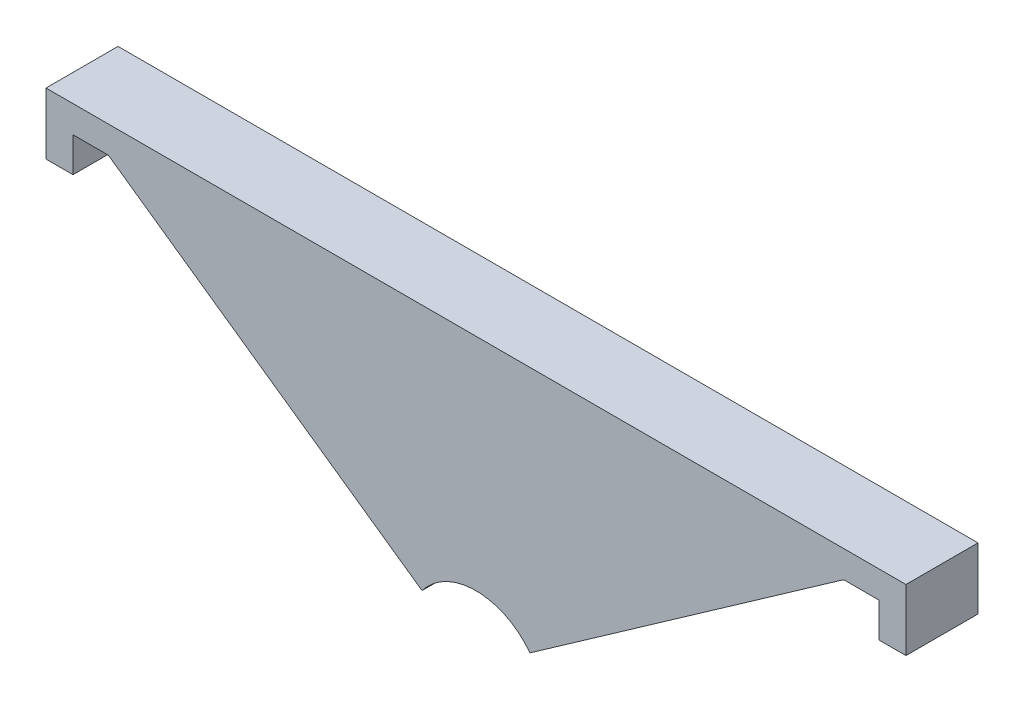
SolidWorks part; units mm, degrees
ref_plane "Plan de face" through (0, 0, 0) normal (0, 0, 1) x (1, 0, 0)
ref_plane "Plan de dessus" through (0, 0, 0) normal (0, 1, 0) x (1, 0, 0)
ref_plane "Plan de droite" through (0, 0, 0) normal (1, 0, 0) x (0, 0, -1)
sketch "Esquisse1" plane through (0, 0, 0) normal (0, 0, 1) x (1, 0, 0)
  line L0 (0, 0) -> (0, 20.2323) construction
  line L2 (-56.5, 0) -> (-56.5, 5) construction
  line L3 (-56.5, 5) -> (-44.5, 5) construction
  line L4 (-44.5, 13.3425) -> (-44.5, 72.3618) construction
  line L11 (-56.5, 0) -> (-35.792, 0) construction
  line L28 (-13.1159, 49.7073) -> (-44.5, 5) construction
  line L29 (-35.792, 0) -> (-21.7522, 20) construction
  line L30 (35.792, 0) -> (21.7522, 20) construction
  line L31 (13.1159, 49.7073) -> (44.5, 5) construction
  line L32 (56.5, 0) -> (35.792, 0) construction
  line L33 (56.5, 5) -> (44.5, 5) construction
  line L34 (56.5, 0) -> (56.5, 5) construction
  line L35 (-21.7522, 20) -> (21.7522, 20) construction
  line L36 (44.5, 5) -> (15.9887, 45.6149) construction
  line L37 (0, 40.5) -> (13.1159, 49.7073) construction
  line L49 (-44.5, 65.6296) -> (-44.5, 69.2189) construction
  line L50 (-44.5, 69.2189) -> (-40.9107, 69.2189) construction
  line L51 (-40.9107, 69.2189) -> (-13.1159, 49.7073) construction
  line L52 (-15.9887, 45.6149) -> (-44.5, 65.6296) construction
  line L54 (-44.5, 5) -> (-15.9887, 45.6149) construction
  line L55 (-13.1159, 49.7073) -> (-6.1385, 44.8092) construction
  line L56 (6.1385, 44.8092) -> (13.1159, 49.7073) construction
  line L57 (44.5, 65.6296) -> (44.5, 69.2189) construction
  line L58 (44.5, 69.2189) -> (40.9107, 69.2189) construction
  line L59 (15.9887, 45.6149) -> (44.5, 65.6296) construction
  line L60 (40.9107, 69.2189) -> (13.1159, 49.7073) construction
  line L61 (-17.0873, 35.3475) -> (-25.8445, 22.8728) construction
  line L62 (-25.8445, 22.8728) -> (-3.3233, 22.8728) construction
  line L63 (-21.7522, 20) -> (-29.9368, 25.7456) construction
  line L64 (-3.3233, 22.8728) -> (-3.3233, 25.8728) construction
  line L65 (-17.0873, 35.3475) -> (-14.0873, 35.3475) construction
  line L66 (0, 40.5) -> (0, 56.525) construction
  line L67 (17.0873, 35.3475) -> (14.0873, 35.3475) construction
  line L68 (3.3233, 22.8728) -> (3.3233, 25.8728) construction
  line L69 (25.8445, 22.8728) -> (3.3233, 22.8728) construction
  line L70 (17.0873, 35.3475) -> (25.8445, 22.8728) construction
  circle A1 centre (0, 40.5) radius 11.025 construction
  arc A3 (13.1159, 49.7073) -> (-13.1159, 49.7073) centre (0, 40.5) ccw construction
  circle A5 centre (0, 40.5) radius 7 construction
  arc A6 (-6.1385, 44.8092) -> (6.1385, 44.8092) centre (0, 40.5) ccw construction
  arc A7 (-3.3233, 25.8728) -> (-14.0873, 35.3475) centre (0, 40.5) cw construction
  arc A8 (3.3233, 25.8728) -> (14.0873, 35.3475) centre (0, 40.5) ccw construction
  point P17 (0, 20)
  dimension "D1" = 22.05
  dimension "D5" = 5
  dimension "D9" = 14
  dimension "D10" = 0.5
  dimension "D12" = 15
  dimension "D2" = 40.5
  dimension "D3" = 5
  dimension "D4" = 12
  dimension "D6" = 10
  dimension "D7" = 56.5
  dimension "D8" = 20
  dimension "D11" = 5
  dimension "D13" = 3
sketch "Esquisse2" plane through (0, 0, 0) normal (0, 0, 1) x (1, 0, 0)
  line L0 (-47.75, 65.6296) -> (-44.75, 65.6296)
  line L1 (0, 40.5) -> (0, 56.525) construction
  line L2 (-44.75, 65.6296) -> (-44.75, 69.4689)
  line L3 (-44.75, 69.4689) -> (-40.8317, 69.4689)
  line L4 (-40.8317, 69.4689) -> (-5.9914, 45.0114)
  line L5 (-40.9107, 69.2189) -> (-13.1159, 49.7073) construction
  line L6 (-44.5, 69.2189) -> (-40.9107, 69.2189) construction
  line L7 (-44.5, -199986.6575) -> (-44.5, 200072.3618) construction
  line L8 (-47.75, 65.6296) -> (-47.75, 72.4689)
  line L9 (47.75, 72.4689) -> (-47.75, 72.4689)
  line L10 (0, -200000) -> (0, 200020.2323) construction
  line L11 (47.75, 65.6296) -> (47.75, 72.4689)
  line L12 (40.8317, 69.4689) -> (5.9914, 45.0114)
  line L13 (44.75, 69.4689) -> (40.8317, 69.4689)
  line L14 (44.75, 65.6296) -> (44.75, 69.4689)
  line L15 (47.75, 65.6296) -> (44.75, 65.6296)
  arc A0 (5.9914, 45.0114) -> (-5.9914, 45.0114) centre (0, 40.5) ccw
  arc A1 (-6.1385, 44.8092) -> (6.1385, 44.8092) centre (0, 40.5) ccw construction
  point P18 (0, 72.4689)
  dimension "D1" = 0.25
  dimension "D2" = 0.25
  dimension "D3" = 0.25
  dimension "D4" = 3
  dimension "D5" = 3
extrude "Boss.-Extru.1" add sketch "Esquisse2" along normal blind 8
